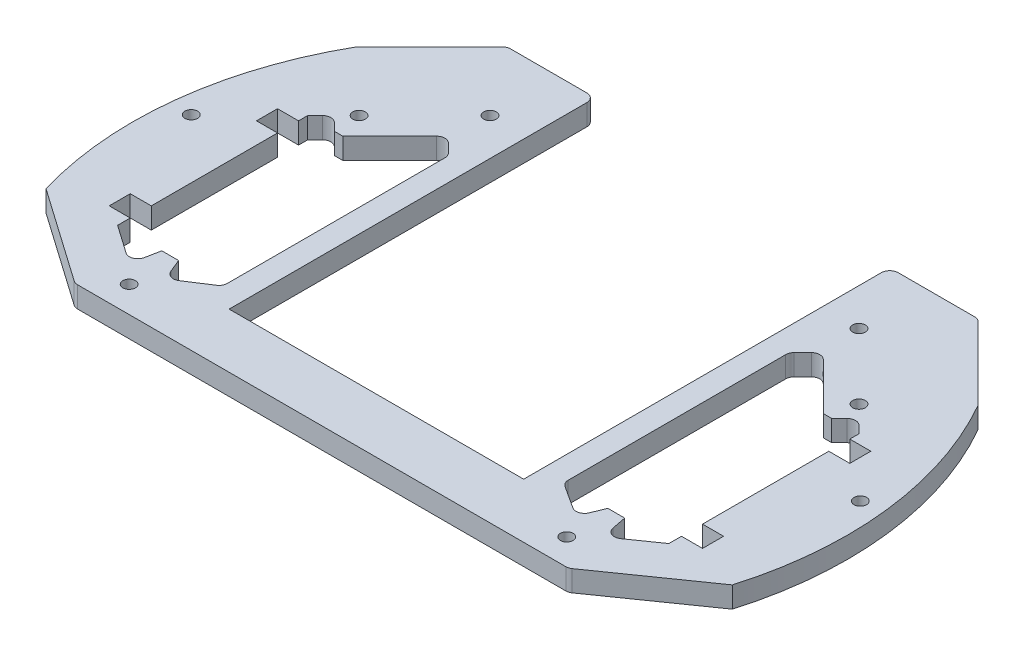
SolidWorks part; units mm, degrees
ref_plane "Front Plane" through (0, 0, 0) normal (0, 0, 1) x (1, 0, 0)
ref_plane "Top Plane" through (0, 0, 0) normal (0, 1, 0) x (1, 0, 0)
ref_plane "Right Plane" through (0, 0, 0) normal (1, 0, 0) x (0, 0, -1)
sketch "Sketch1" plane through (0, 0, 0) normal (0, 1, 0) x (1, 0, 0)
  line L0 (-58.656, -40) -> (-81.5505, -23.9691)
  line L1 (-65.5, 22.1812) -> (-65.5, 20)
  line L2 (-73.8099, 42.1556) -> (-55.9655, 60)
  line L3 (-35, 60) -> (-35, -27)
  line L4 (-35, -27) -> (0, -27)
  line L5 (0, -40) -> (-58.656, -40)
  line L6 (-59.397, 28.2843) -> (-43.8406, 43.8406) construction
  line L7 (-51.9976, -33.7676) -> (-63.9796, -15.3169) construction
  line L8 (-55.9655, 60) -> (-35, 60)
  line L9 (0, 0) -> (-85, 0) construction
  line L10 (-43.8406, 43.8406) -> (0, 0) construction
  line L11 (-51.9976, -33.7676) -> (0, 0) construction
  line L12 (-59.096, 22.1) -> (-57.096, 22.1)
  line L13 (-65.5, 15) -> (-65.5, -15)
  line L14 (-55, -23) -> (-51, -23)
  line L15 (-40.5, 30.6005) -> (-40.5, -23)
  line L16 (-53, 22.1) -> (-53, -23) construction
  line L17 (-65.5, 22.1812) -> (-62.3386, 25.3426)
  line L18 (-62.3386, 25.3426) -> (-59.096, 22.1)
  line L19 (-57.096, 22.1) -> (-44.5477, 34.6482)
  line L20 (-44.5477, 34.6482) -> (-40.5, 30.6005)
  line L21 (-65.5, -23) -> (-56.2568, -29.4721)
  line L22 (-56.2568, -29.4721) -> (-55, -23)
  line L23 (-51, -23) -> (-48.7962, -28.3876)
  line L24 (-48.7962, -28.3876) -> (-40.5, -23)
  line L25 (-65, 52) -> (-27, 80) construction
  line L26 (-27, 80) -> (0, 80) construction
  line L27 (0, 80) -> (0, 4) construction
  line L28 (0, 4) -> (-65, 4) construction
  line L29 (-65, 52) -> (-65, 4) construction
  line L30 (0, -27) -> (0, -40)
  line L39 (-65.5, 20) -> (-70.5, 20)
  line L40 (-70.5, 20) -> (-70.5, 15)
  line L41 (-70.5, 15) -> (-65.5, 15)
  line L42 (-65.5, -23) -> (-65.5, -20)
  line L43 (-65.5, -20) -> (-70.5, -20)
  line L44 (-70.5, -20) -> (-70.5, -15)
  line L45 (-70.5, -15) -> (-65.5, -15)
  circle A0 centre (0, 0) radius 85 construction
  circle A1 centre (-43.8406, 43.8406) radius 1.5
  circle A2 centre (-51.9976, -33.7676) radius 1.5
  circle A3 centre (-59.397, 28.2843) radius 1.5
  circle A4 centre (-63.9796, -15.3169) radius 1.5 construction
  arc A5 (-81.5505, -23.9691) -> (-73.8099, 42.1556) centre (0, 0) cw
  circle A6 centre (-79.5, 8.5) radius 1.5
  dimension "D7" = 3
  dimension "D17" = 170
  dimension "D20" = 12.5
  dimension "D4" = 40
  dimension "D5" = 125
  dimension "D6" = 8.5
  dimension "D8" = 62
  dimension "D9" = 22
  dimension "D10" = 22
  dimension "D11" = 25
  dimension "D12" = 45.1
  dimension "D13" = 65
  dimension "D14" = 45
  dimension "D15" = 33
  dimension "D16" = 23
  dimension "D18" = 20
  dimension "D19" = 60
  dimension "D21" = 5
  dimension "D22" = 5
  dimension "D23" = 4
  dimension "D24" = 6
  dimension "D25" = 15
  dimension "D26" = 40.5
  dimension "D27" = 10
  dimension "D28" = 27
  dimension "D29" = 35
  dimension "D30" = 38
  dimension "D31" = 28
  dimension "D32" = 80
  dimension "D33" = 76
  dimension "D34" = 2
  dimension "D35" = 79.5
  dimension "D38" = 20
  dimension "D40" = 5
  dimension "D41" = 30
extrude "Boss-Extrude1" add sketch "Sketch1" along normal blind 5
fillet "Fillet1" radius 2 6 edges at (-40.5, 2.5, 23) (-48.7962, 2.5, 28.3876) (-56.2568, 2.5, 29.4721) (-62.3386, 2.5, -25.3426) (-40.5, 2.5, -30.6005) (-44.5477, 2.5, -34.6482)
mirror "Mirror1" about plane through (0, 0, 0) normal (1, 0, 0) of "Boss-Extrude1", "Fillet1"
fillet "Fillet2" radius 2 6 edges at (-55.9655, 2.5, -60) (55.9655, 2.5, -60) (-58.656, 2.5, 40) (58.656, 2.5, 40) (35, 2.5, -60) (-35, 2.5, -60)
